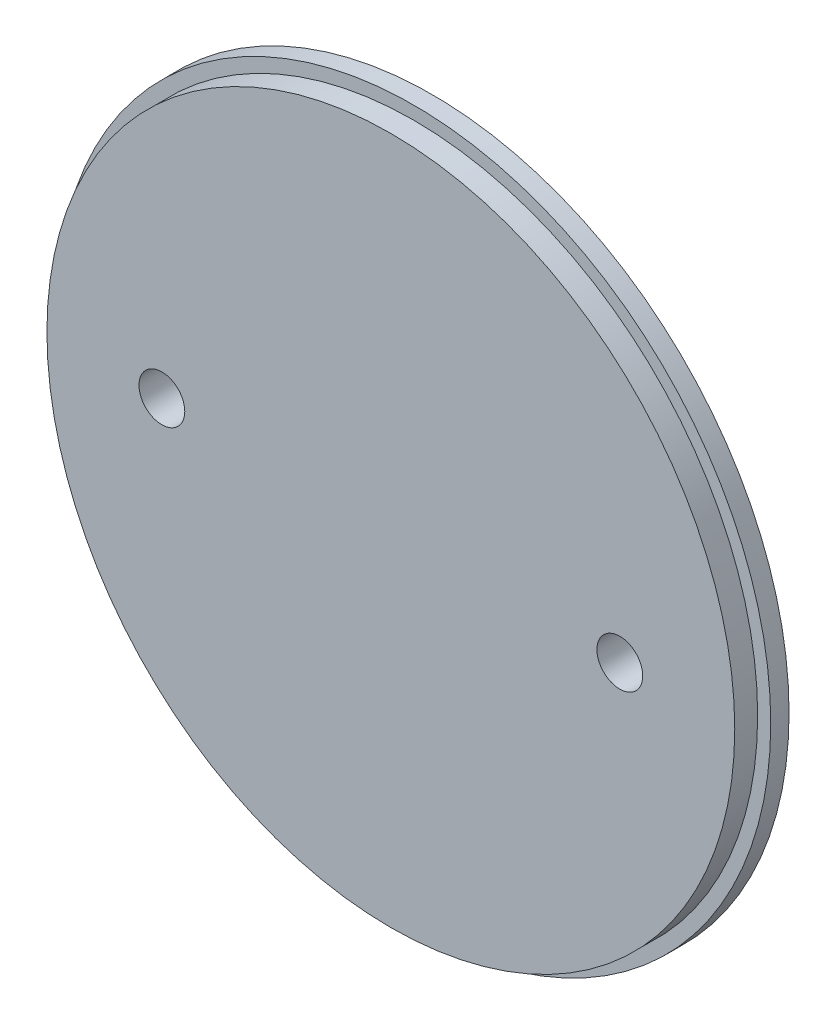
SolidWorks part; units mm, degrees
ref_plane "Front Plane" through (0, 0, 0) normal (0, 0, 1) x (1, 0, 0)
ref_plane "Top Plane" through (0, 0, 0) normal (0, 1, 0) x (1, 0, 0)
ref_plane "Right Plane" through (0, 0, 0) normal (1, 0, 0) x (0, 0, -1)
sketch "Sketch1" plane through (0, 0, 0) normal (0, 0, 1) x (1, 0, 0)
  circle A0 centre (0, 0) radius 49.5046
  dimension "D1" = 99.0092
extrude "Boss-Extrude1" add sketch "Sketch1" along normal blind 2.54
sketch "Sketch2" plane through (0, 0, 2.54) normal (0, 0, 1) x (1, 0, 0)
  circle A0 centre (0, 0) radius 47.6885
  dimension "D1" = 95.377
extrude "Boss-Extrude2" add sketch "Sketch2" along normal blind 3.175
sketch "Sketch3" plane through (0, 0, 5.715) normal (0, 0, 1) x (1, 0, 0)
  circle A0 centre (-31.75, 0) radius 3.175
  circle A1 centre (31.75, 0) radius 3.175
  dimension "D1" = 6.35
  dimension "D2" = 6.35
  dimension "D3" = 63.5
  dimension "D4" = 31.75
extrude "Cut-Extrude1" cut sketch "Sketch3" against normal through all
